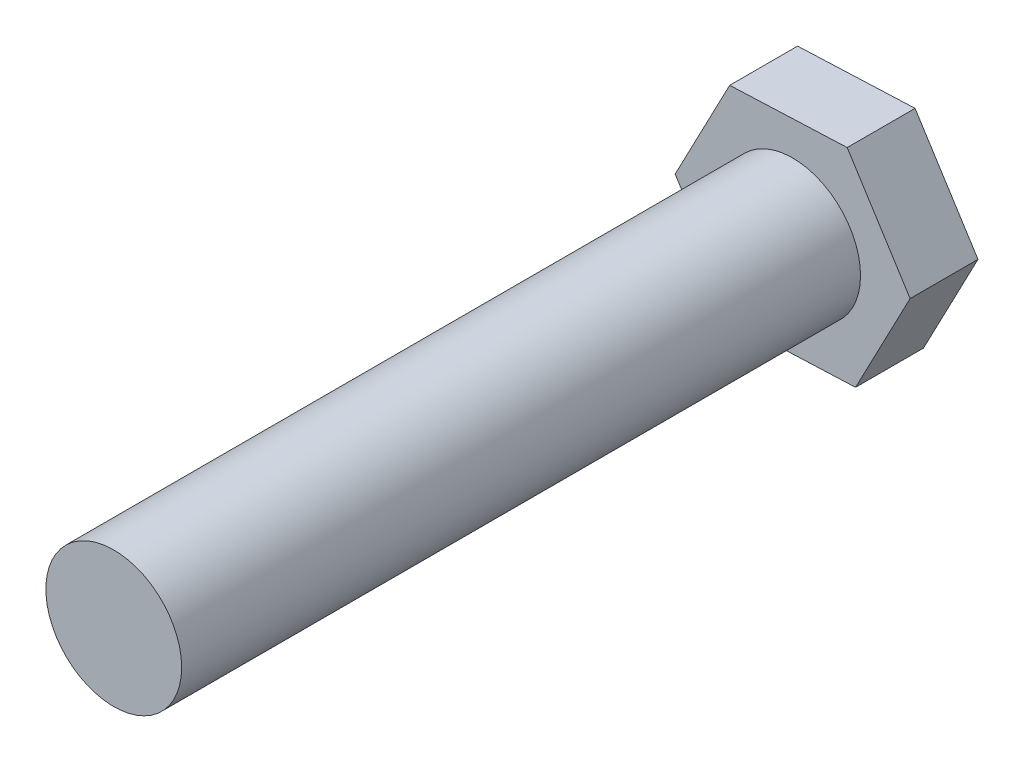
SolidWorks part; units mm, degrees
ref_plane "Front Plane" through (0, 0, 0) normal (0, 0, 1) x (1, 0, 0)
ref_plane "Top Plane" through (0, 0, 0) normal (0, 1, 0) x (1, 0, 0)
ref_plane "Right Plane" through (0, 0, 0) normal (1, 0, 0) x (0, 0, -1)
sketch "Sketch1" plane through (0, 0, 0) normal (0, 0, 1) x (1, 0, 0)
  line L1 (1.8539, -2.9262) -> (3.4612, 0.1424)
  line L2 (3.4612, 0.1424) -> (1.6072, 3.0687)
  line L3 (1.6072, 3.0687) -> (-1.8539, 2.9262)
  line L4 (-1.8539, 2.9262) -> (-3.4612, -0.1424)
  line L5 (-3.4612, -0.1424) -> (-1.6072, -3.0687)
  line L6 (-1.6072, -3.0687) -> (1.8539, -2.9262)
  circle A0 centre (0, 0) radius 3 construction
  dimension "D1" = 6
extrude "Boss-Extrude1" add sketch "Sketch1" along normal blind 2
sketch "Sketch2" plane through (0, 0, 2) normal (0, 0, 1) x (1, 0, 0)
  circle A0 centre (0, 0) radius 2
  dimension "D1" = 4
extrude "Boss-Extrude2" add sketch "Sketch2" along normal blind 20
